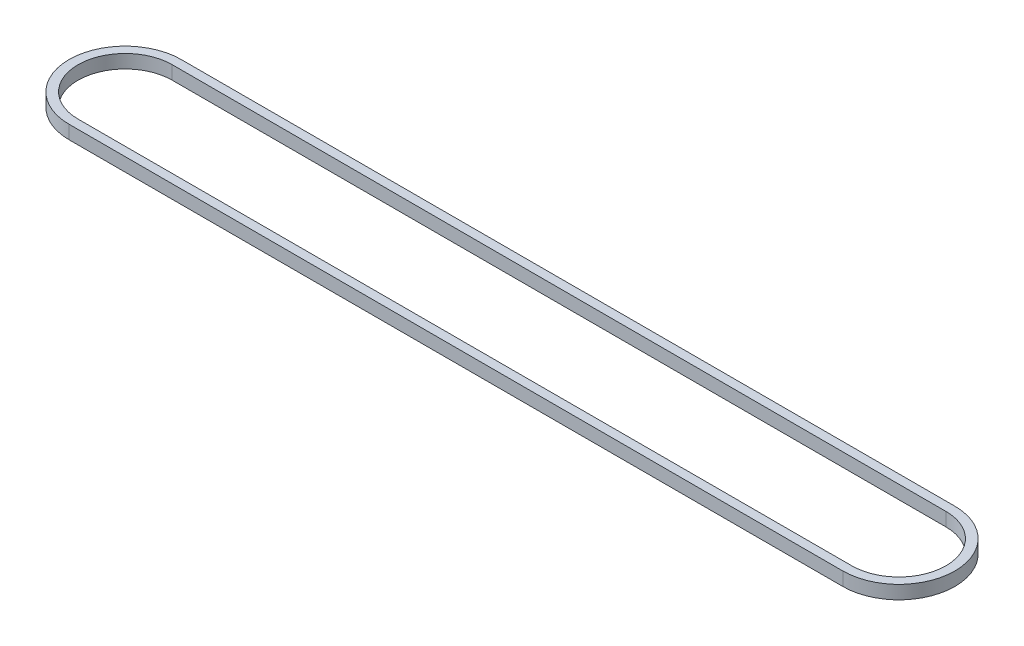
SolidWorks part; units mm, degrees
ref_plane "Front Plane" through (0, 0, 0) normal (0, 0, 1) x (1, 0, 0)
ref_plane "Top Plane" through (0, 0, 0) normal (0, 1, 0) x (1, 0, 0)
ref_plane "Right Plane" through (0, 0, 0) normal (1, 0, 0) x (0, 0, -1)
sketch "Sketch1" plane through (0, 0, 0) normal (0, 1, 0) x (1, 0, 0)
  line L0 (-32.6689, 12.5) -> (139.8311, 12.5)
  line L1 (-32.6689, -12.5) -> (139.8311, -12.5)
  line L2 (-32.6689, 10.5) -> (139.8311, 10.5)
  line L3 (-32.6689, -10.5) -> (139.8311, -10.5)
  arc A0 (-32.6689, 12.5) -> (-32.6689, -12.5) centre (-32.6689, 0) ccw
  arc A1 (139.8311, -12.5) -> (139.8311, 12.5) centre (139.8311, 0) ccw
  arc A2 (139.8311, -10.5) -> (139.8311, 10.5) centre (139.8311, 0) ccw
  arc A3 (-32.6689, 10.5) -> (-32.6689, -10.5) centre (-32.6689, 0) ccw
  point P1 (-123.8489, 37.2261)
  dimension "D1" = 25
  dimension "D2" = 2
  dimension "D3" = 172.5
extrude "Boss-Extrude1" add sketch "Sketch1" along normal blind 3
